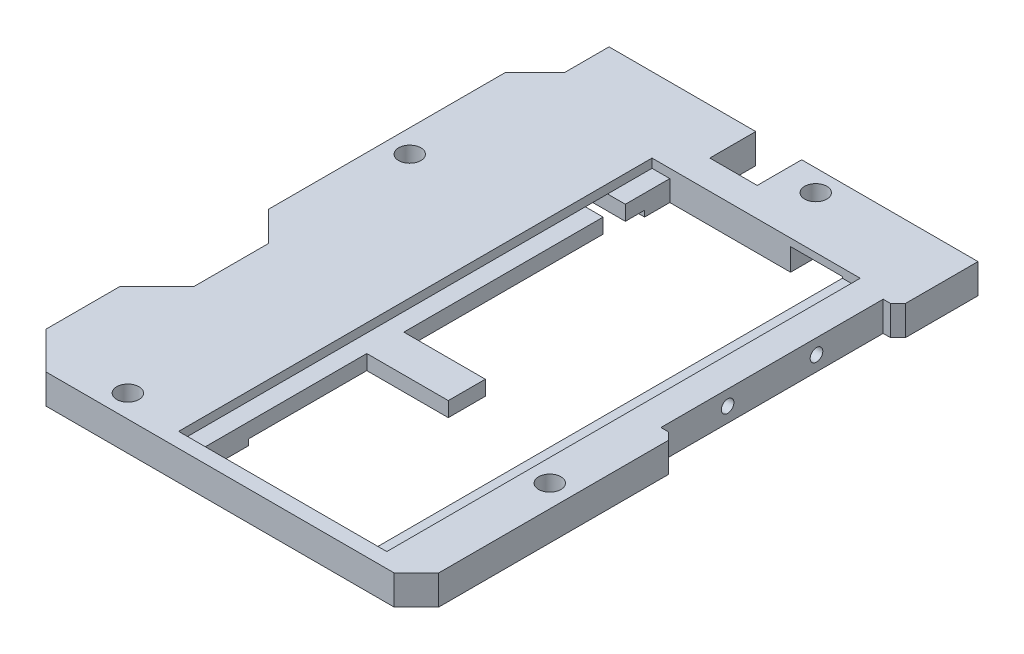
SolidWorks part; units mm, degrees
ref_plane "前视基准面" through (0, 0, 0) normal (0, 0, 1) x (1, 0, 0)
ref_plane "上视基准面" through (0, 0, 0) normal (0, 1, 0) x (1, 0, 0)
ref_plane "右视基准面" through (0, 0, 0) normal (1, 0, 0) x (0, 0, -1)
sketch "草图1" plane through (0, 0, 0) normal (0, 1, 0) x (1, 0, 0)
  line L1 (0, 0) -> (50, 0)
  line L2 (0, 0) -> (0, 76)
  line L3 (0, 76) -> (50, 76)
  line L4 (50, 0) -> (50, 76)
  dimension "D1" = 76
  dimension "D2" = 50
extrude "凸台-拉伸1" add sketch "草图1" along normal blind 4
sketch "草图3" plane through (0, 4, 0) normal (0, 1, 0) x (1, 0, 0)
  line L0 (0, 0) -> (-5, 5)
  line L1 (-5, 5) -> (-5, 15)
  line L2 (-5, 15) -> (0, 20)
  line L3 (0, 76) -> (0, 0) construction
  line L4 (0, 20) -> (0, 0)
  line L5 (0, 30) -> (-4, 34)
  line L6 (-4, 34) -> (-4, 66)
  line L7 (-4, 66) -> (0, 70)
  line L8 (0, 70) -> (0, 30)
  line L9 (0, 0) -> (50, 0) construction
  dimension "D1" = 45
  dimension "D2" = 45
  dimension "D3" = 5
  dimension "D4" = 20
  dimension "D5" = 45
  dimension "D6" = 45
  dimension "D7" = 4
  dimension "D8" = 30
  dimension "D9" = 40
extrude "凸台-拉伸2" add sketch "草图3" against normal blind 4
sketch "草图4" plane through (0, 4, 0) normal (0, 1, 0) x (1, 0, 0)
  line L0 (50, 76) -> (0, 76) construction
  line L1 (19.8, 76) -> (26.2, 76)
  line L2 (19.8, 76) -> (19.8, 69.8)
  line L3 (19.8, 69.8) -> (26.2, 69.8)
  line L4 (26.2, 76) -> (26.2, 69.8)
  line L5 (0, 76) -> (0, 70) construction
  dimension "D1" = 19.8
  dimension "D2" = 6.4
  dimension "D3" = 6.2
extrude "切除-拉伸1" cut sketch "草图4" against normal blind 4
chamfer "倒角1" distance 3 angle 45 1 edges at (50, 2, 0)
sketch "草图6" plane through (0, 4, 0) normal (0, 1, 0) x (1, 0, 0)
  line L0 (50, 3) -> (50, 76) construction
  line L1 (50, 65) -> (48, 65)
  line L2 (50, 65) -> (50, 35)
  line L3 (50, 35) -> (48, 35)
  line L4 (48, 65) -> (48, 35)
  line L5 (0, 0) -> (47, 0) construction
  dimension "D1" = 2
  dimension "D2" = 30
  dimension "D3" = 35
extrude "切除-拉伸3" cut sketch "草图6" against normal through all
sketch "草图7" plane through (0, 4, 0) normal (0, 1, 0) x (1, 0, 0)
  line L0 (0, 0) -> (47, 0) construction
  line L1 (15.9, 2) -> (44, 2)
  line L2 (15.9, 2) -> (15.9, 65.9)
  line L3 (15.9, 65.9) -> (44, 65.9)
  line L4 (44, 2) -> (44, 65.9)
  line L5 (50, 3) -> (50, 35) construction
  dimension "D1" = 2
  dimension "D2" = 6
  dimension "D3" = 28.1
  dimension "D4" = 63.9
extrude "切除-拉伸4" cut sketch "草图7" against normal blind 1.2
sketch "草图8" plane through (0, 2.8, 0) normal (0, 1, 0) x (1, 0, 0)
  line L0 (41.6, 65.9) -> (41.6, 2)
  line L1 (18.3, 65.9) -> (18.3, 30)
  line L2 (44, 2) -> (44, 65.9) construction
  line L3 (15.9, 65.9) -> (15.9, 2) construction
  line L4 (15.9, 65.9) -> (15.9, 2)
  line L5 (15.9, 2) -> (44, 2)
  line L6 (44, 2) -> (44, 65.9)
  line L7 (44, 65.9) -> (15.9, 65.9)
  line L9 (18.3, 2) -> (41.6, 2)
  line L11 (41.6, 65.9) -> (18.3, 65.9)
  line L16 (29.3, 30) -> (29.3, 25)
  line L19 (29.3, 30) -> (18.3, 30)
  line L20 (18.3, 25) -> (18.3, 2)
  line L21 (18.3, 25) -> (29.3, 25)
  dimension "D2" = 2.4
  dimension "D3" = 2.4
  dimension "D4" = 11
  dimension "D5" = 23
  dimension "D6" = 5
  dimension "D1" = 0
extrude "切除-拉伸5" cut sketch "草图8" against normal through all
sketch "草图9" plane through (0, 0, 0) normal (0, -1, 0) x (1, 0, 0)
  line L0 (18.3, -25) -> (18.3, -2) construction
  line L1 (18.3, -65.9) -> (18.3, -30) construction
  line L2 (18.3, -30) -> (29.3, -30) construction
  line L3 (29.3, -30) -> (29.3, -25) construction
  line L4 (29.3, -25) -> (18.3, -25) construction
  line L5 (18.3, -25) -> (18.3, -9)
  line L6 (18.3, -62.5) -> (18.3, -30)
  line L7 (18.3, -30) -> (29.3, -30)
  line L8 (29.3, -30) -> (29.3, -25)
  line L9 (29.3, -25) -> (18.3, -25)
  line L22 (15.2, -62.5) -> (36.9, -62.5) construction
  line L23 (15.2, -62.5) -> (15.2, -67.4) construction
  line L24 (5.8, -67.4) -> (15.2, -67.4) construction
  line L25 (5.8, -62.5) -> (5.8, -67.4) construction
  line L26 (2.4, -62.5) -> (5.8, -62.5) construction
  line L27 (4.4, -61) -> (4.4, -62.5) construction
  line L28 (2.4, -61) -> (4.4, -61) construction
  line L29 (2.4, -9) -> (2.4, -62.5) construction
  line L30 (2.4, -9) -> (25.2001, -9) construction
  line L31 (15.2, -62.5) -> (18.3, -62.5)
  line L32 (15.2, -62.5) -> (15.2, -67.4)
  line L33 (5.8, -67.4) -> (15.2, -67.4)
  line L34 (5.8, -62.5) -> (5.8, -67.4)
  line L35 (4.4, -62.5) -> (5.8, -62.5)
  line L36 (4.4, -61) -> (4.4, -62.5)
  line L37 (2.4, -61) -> (4.4, -61)
  line L38 (2.4, -9) -> (2.4, -61)
  line L39 (2.4, -9) -> (18.3, -9)
extrude "切除-拉伸6" cut sketch "草图9" against normal blind 0.8
sketch "草图10" plane through (48, 0, 0) normal (1, 0, 0) x (0, 0, -1)
  circle A0 centre (44, 2) radius 1.2 construction
  circle A5 centre (44, 2) radius 0.85
  circle A6 centre (56, 2) radius 0.85
  dimension "D1" = 1.7
  dimension "D2" = 1.7
extrude "切除-拉伸7" cut sketch "草图10" against normal blind 3
sketch "草图11" plane through (0, 4, 0) normal (0, 1, 0) x (1, 0, 0)
  circle A0 centre (-0.9, 50) radius 1.5
  circle A1 centre (31, 72.9) radius 1.5
  circle A2 centre (8, 3.05) radius 1.5
  circle A3 centre (47, 21) radius 1.5
  dimension "D1" = 3
extrude "切除-拉伸8" cut sketch "草图11" against normal through all
chamfer "倒角2" distance 1 angle 45 2 edges at (50, 2, -65) (50, 2, -35)
sketch "草图12" plane through (0, 0, 0) normal (0, -1, 0) x (1, 0, 0)
  line L0 (50, -76) -> (26.2, -76) construction
  line L1 (41.6, -65.9) -> (34.6, -65.9)
  line L2 (41.6, -65.9) -> (41.6, -76)
  line L3 (41.6, -76) -> (34.6, -76)
  line L4 (34.6, -65.9) -> (34.6, -76)
  dimension "D1" = 7
extrude "切除-拉伸9" cut sketch "草图12" against normal blind 3
chamfer "倒角3" distance 0.2 angle 45 4 edges at (26.2, 2, -76) (45.8, 0, -76) (50, 2, -76) (38.1, 4, -76)
sketch "草图13" plane through (0, 0.8, 0) normal (0, -1, 0) x (1, 0, 0)
  line L0 (5.8, -67.4) -> (15.2, -67.4) construction
  line L1 (15.2, -67.4) -> (15.2, -62.5) construction
  line L2 (5.8, -62.5) -> (5.8, -67.4) construction
  line L3 (5.8, -67.4) -> (15.2, -67.4)
  line L4 (15.2, -67.4) -> (15.2, -65.4)
  line L5 (5.8, -65.4) -> (5.8, -67.4)
  line L6 (15.2, -65.4) -> (12.2, -65.4)
  line L7 (18.3, -62.5) -> (18.3, -30) construction
  line L8 (18.3, -56.9) -> (8.8, -56.9)
  line L9 (18.3, -56.9) -> (18.3, -59.9)
  line L10 (18.3, -59.9) -> (12.2, -59.9)
  line L11 (8.8, -56.9) -> (8.8, -59.9558)
  line L12 (8.8, -65.4) -> (5.8, -65.4)
  line L14 (8.8, -59.9558) -> (8.8, -65.4)
  line L16 (12.2, -59.9) -> (12.2, -65.4)
  line L17 (15.2, -62.5) -> (18.3, -62.5) construction
  dimension "D1" = 2
  dimension "D2" = 3
  dimension "D3" = 3
  dimension "D4" = 3
  dimension "D5" = 2.6
extrude "切除-拉伸10" cut sketch "草图13" against normal blind 2
